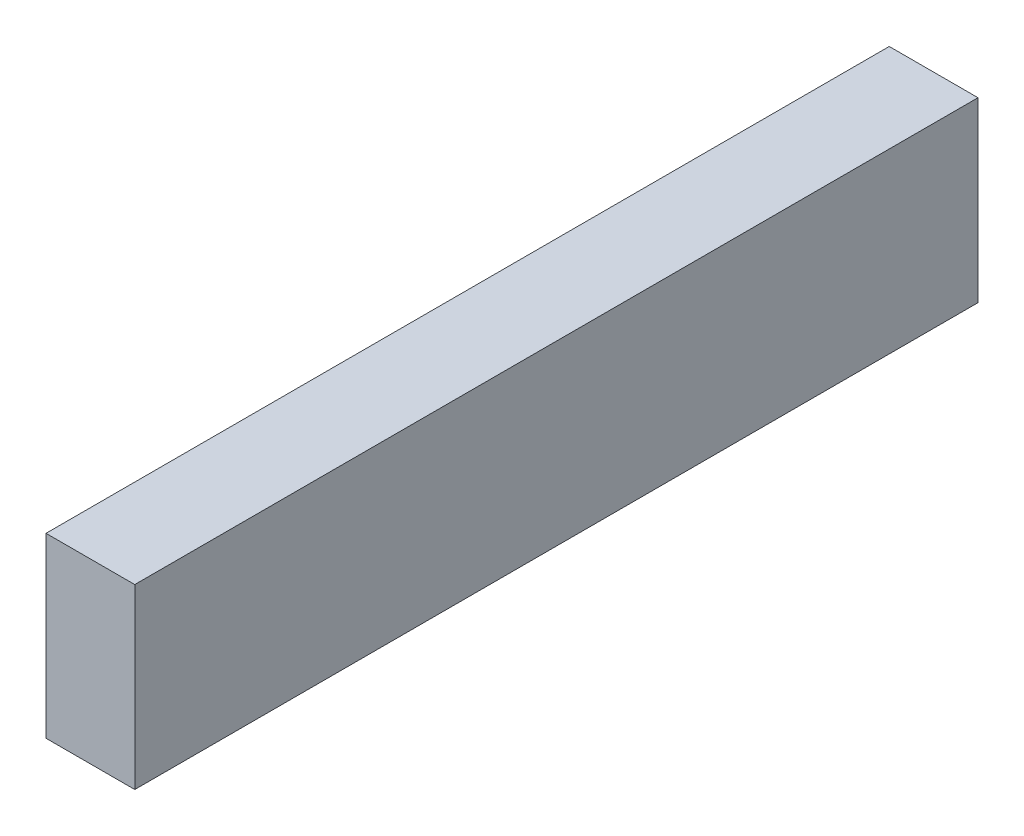
SolidWorks part; units mm, degrees
ref_plane "Front Plane" through (0, 0, 0) normal (0, 0, 1) x (1, 0, 0)
ref_plane "Top Plane" through (0, 0, 0) normal (0, 1, 0) x (1, 0, 0)
ref_plane "Right Plane" through (0, 0, 0) normal (1, 0, 0) x (0, 0, -1)
sketch "Sketch1" plane through (0, 3, 0) normal (0, -1, 0) x (1, 0, 0)
  line L1 (142.5, -75) -> (132.5, -75)
  line L2 (142.5, -75) -> (142.5, 20)
  line L3 (142.5, 20) -> (132.5, 20)
  line L4 (132.5, -75) -> (132.5, 20)
  dimension "D1" = 10
  dimension "D2" = 95
extrude "Boss-Extrude1" add sketch "Sketch1" along normal blind 20
